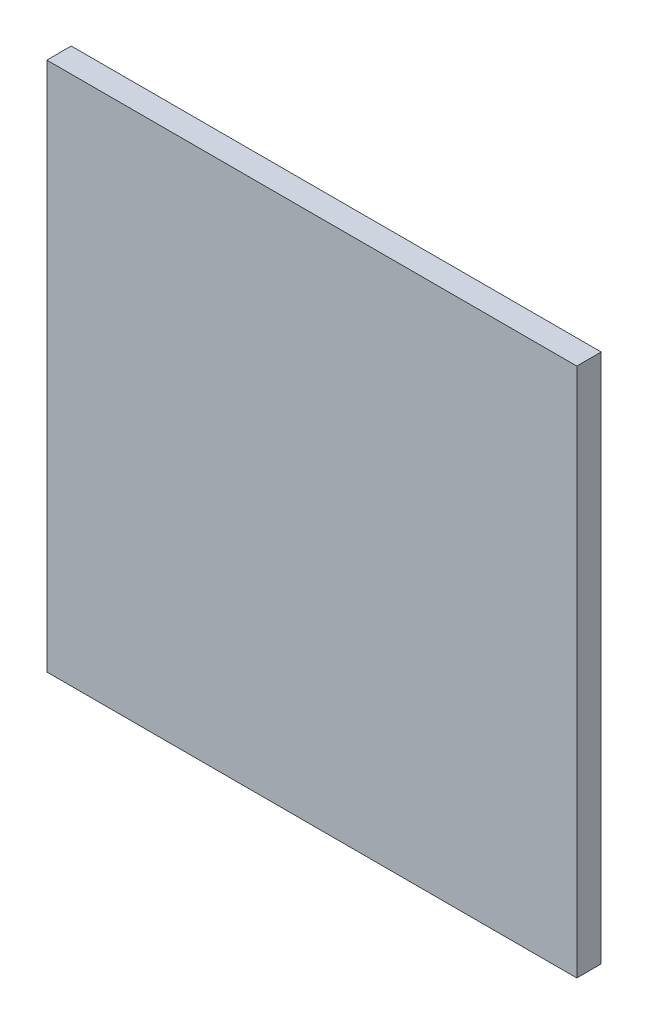
SolidWorks part; units mm, degrees
ref_plane "前视基准面" through (0, 0, 0) normal (0, 0, 1) x (1, 0, 0)
ref_plane "上视基准面" through (0, 0, 0) normal (0, 1, 0) x (1, 0, 0)
ref_plane "右视基准面" through (0, 0, 0) normal (1, 0, 0) x (0, 0, -1)
sketch "草图1" plane through (0, 0, 0) normal (0, 0, 1) x (1, 0, 0)
  line L0 (177.4959, 98.1265) -> (227.4959, 98.1265)
  line L1 (177.4959, 148.1265) -> (227.4959, 148.1265)
  line L2 (177.4959, 148.1265) -> (177.4959, 98.1265)
  line L3 (227.4959, 148.1265) -> (227.4959, 98.1265)
  dimension "D1" = 50
  dimension "D2" = 50
extrude "凸台-拉伸1" add sketch "草图1" along normal blind 2.3
